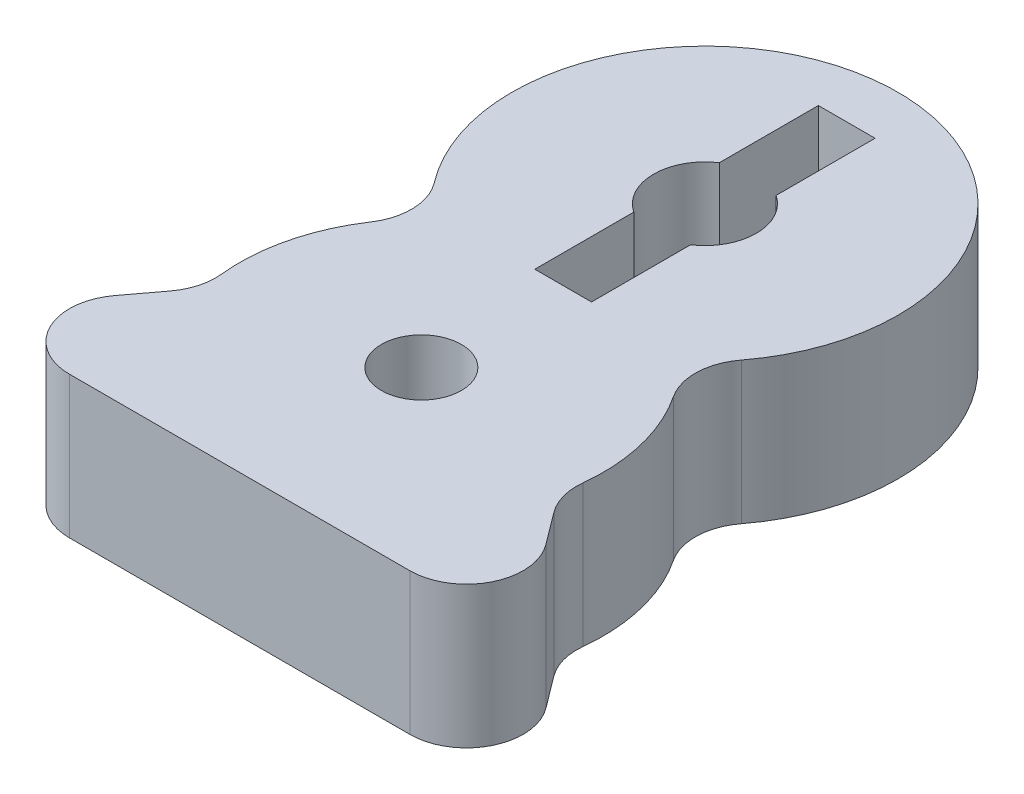
SolidWorks part; units mm, degrees
ref_plane "Front" through (0, 0, 0) normal (0, 0, 1) x (1, 0, 0)
ref_plane "Top" through (0, 0, 0) normal (0, 1, 0) x (1, 0, 0)
ref_plane "Right" through (0, 0, 0) normal (1, 0, 0) x (0, 0, -1)
sketch "Sketch1" plane through (0, 0, 0) normal (0, 1, 0) x (1, 0, 0)
  line L0 (-12.7, -8.1407) -> (12.7, -8.1407)
  line L1 (-12.7, -8.1407) -> (-7.9413, -1.7907)
  line L2 (12.7, -8.1407) -> (7.9413, -1.7907)
  line L3 (-7.9413, -1.7907) -> (7.9413, -1.7907) construction
  circle A0 centre (0, 0) radius 1.7907
  circle A1 centre (0, 12.7) radius 2.2987
  arc A2 (-5.4864, 6.0142) -> (-7.9413, -1.7907) centre (0, 0) ccw
  arc A3 (5.4864, 6.0142) -> (-5.4864, 6.0142) centre (0, 12.7) ccw
  arc A4 (7.9413, -1.7907) -> (5.4864, 6.0142) centre (0, 0) ccw
  dimension "D1" = 3.5814
  dimension "D2" = 4.5974
  dimension "D4" = 6.35
  dimension "D5" = 6.35
  dimension "D3" = 12.7
  dimension "D6" = 6.35
  dimension "D7" = 25.4
extrude "Boss-Extrude1" add sketch "Sketch1" along normal blind 6.35
fillet "Fillet1" radius 2.54 6 edges at (12.7, 3.175, 8.1407) (-12.7, 3.175, 8.1407) (-7.9413, 3.175, 1.7907) (-5.4864, 3.175, -6.0142) (5.4864, 3.175, -6.0142) (7.9413, 3.175, 1.7907)
sketch "Sketch2" plane through (0, 6.35, 0) normal (0, 1, 0) x (1, 0, 0)
  line L1 (-1.27, 19.05) -> (1.27, 19.05)
  line L2 (-1.27, 19.05) -> (-1.27, 6.35)
  line L3 (-1.27, 6.35) -> (1.27, 6.35)
  line L4 (1.27, 19.05) -> (1.27, 6.35)
  line L5 (-1.27, 19.05) -> (1.27, 6.35) construction
  line L6 (-1.27, 6.35) -> (1.27, 19.05) construction
  point P0 (0, 12.7)
  dimension "D1" = 12.7
  dimension "D2" = 2.54
extrude "Cut-Extrude1" cut sketch "Sketch2" against normal up to surface (6.35 mm away) up to face at (0, 0, 1.7907)
